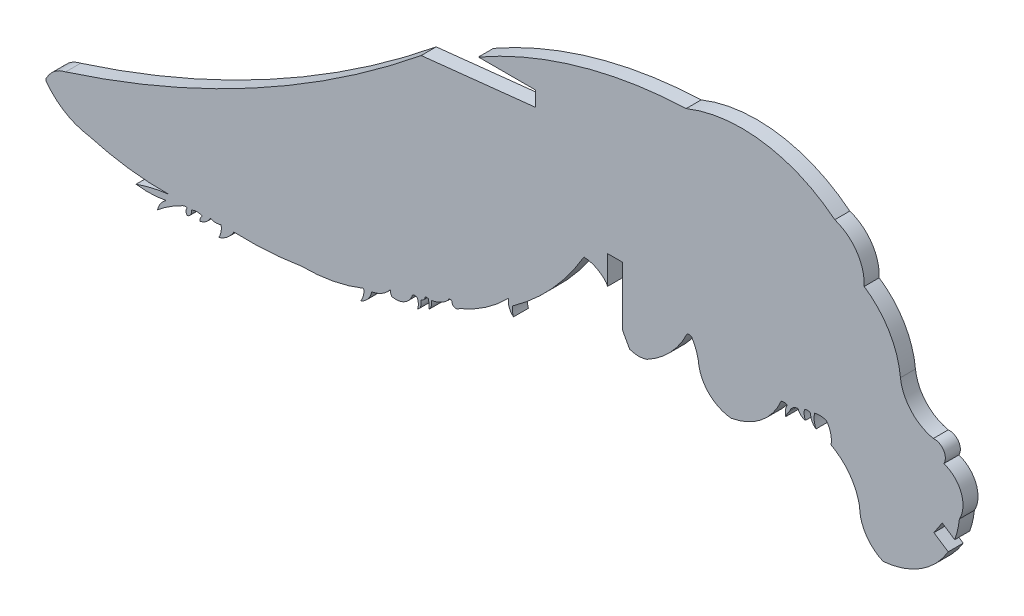
SolidWorks part; units mm, degrees
ref_plane "Front Plane" through (0, 0, 0) normal (0, 0, 1) x (1, 0, 0)
ref_plane "Top Plane" through (0, 0, 0) normal (0, 1, 0) x (1, 0, 0)
ref_plane "Right Plane" through (0, 0, 0) normal (1, 0, 0) x (0, 0, -1)
sketch "Sketch1" plane through (0, 0, 0) normal (0, 0, 1) x (1, 0, 0)
  line L0 (52.7499, 70.1318) -> (64.3715, 71.3815)
  line L1 (64.3715, 71.3815) -> (64.3715, 72.9055)
  line L2 (64.3715, 72.9055) -> (58.5607, 72.9055)
  arc A0 (16.6357, 50.6377) -> (52.7499, 70.1318) centre (-16.879, 155.9248) ccw
  arc A1 (58.5607, 72.9055) -> (79.6651, 78.9249) centre (81.4568, 32.6366) cw
  arc A2 (79.6651, 78.9249) -> (94.7592, 76.6935) centre (85.3161, 64.9832) cw
  arc A3 (94.7592, 76.6935) -> (97.7466, 72.3165) centre (93.3504, 72.5239) cw
  arc A4 (97.7466, 72.3165) -> (101.4288, 66.1332) centre (93.0407, 65.3261) cw
  arc A5 (101.4288, 66.1332) -> (104.7636, 62.451) centre (105.6642, 66.6179) ccw
  arc A6 (104.7636, 62.451) -> (105.8344, 60.7757) centre (104.878, 61.3443) cw
  arc A7 (105.8344, 60.7757) -> (107.4136, 56.6954) centre (104.9626, 58.0925) cw
  arc A8 (107.4136, 56.6954) -> (99.6697, 49.0898) centre (98.9655, 57.552) cw
  arc A9 (99.6697, 49.0898) -> (97.2774, 52.7389) centre (101.2688, 52.747) cw
  arc A10 (97.2774, 52.7389) -> (94.3777, 56.6954) centre (91.6801, 51.6775) ccw
  arc A11 (94.3777, 56.6954) -> (93.9114, 58.6026) centre (91.9396, 57.1099) ccw
  arc A12 (93.9114, 58.6026) -> (92.7155, 58.6578) centre (93.2218, 56.6439) ccw
  arc A13 (92.7155, 58.6578) -> (92.8575, 57.3378) centre (94.569, 58.1895) ccw
  arc A14 (92.8575, 57.3378) -> (92.3084, 58.4414) centre (93.5533, 58.3724) cw
  arc A15 (92.3084, 58.4414) -> (91.6801, 58.4762) centre (91.9646, 57.9232) ccw
  arc A16 (91.6801, 58.4762) -> (91.7794, 57.552) centre (93.0965, 58.1611) ccw
  arc A17 (91.7794, 57.552) -> (91.0329, 58.2279) centre (91.9297, 58.4683) cw
  arc A18 (91.0329, 58.2279) -> (90.1702, 57.5697) centre (91.1217, 57.2172) ccw
  arc A19 (90.1702, 57.5697) -> (89.7788, 56.8792) centre (91.7217, 56.2341) ccw
  arc A20 (89.7788, 56.8792) -> (89.9407, 57.9851) centre (91.1279, 57.2465) cw
  arc A21 (89.9407, 57.9851) -> (89.3088, 58.0044) centre (89.6037, 57.3052) ccw
  arc A22 (89.3088, 58.0044) -> (84.2372, 53.9696) centre (83.0444, 60.6738) cw
  arc A23 (84.2372, 53.9696) -> (80.9686, 56.8792) centre (84.55, 57.6117) cw
  arc A24 (80.9686, 56.8792) -> (80.2253, 59.1108) centre (75.9214, 56.4377) ccw
  arc A25 (80.2253, 59.1108) -> (79.7482, 59.1337) centre (79.9709, 58.7913) ccw
  arc A26 (79.7482, 59.1337) -> (75.7005, 54.8813) centre (71.2227, 63.1961) cw
  arc A27 (75.7005, 54.8813) -> (73.9294, 54.8813) centre (74.8149, 57.3024) cw
  arc A28 (73.9294, 54.8813) -> (71.5552, 59.5421) centre (124.0127, 83.3286) cw
  arc A29 (71.5552, 59.5421) -> (69.2804, 60.6738) centre (69.0881, 57.4352) ccw
  arc A30 (69.2804, 60.6738) -> (62.0239, 52.7389) centre (47.2299, 73.5536) cw
  arc A31 (62.0239, 52.7389) -> (62.1223, 51.8245) centre (63.9478, 52.4833) ccw
  arc A32 (62.1223, 51.8245) -> (61.6182, 53.2211) centre (63.0669, 52.9546) cw
  arc A33 (61.6182, 53.2211) -> (56.6231, 49.804) centre (51.0045, 63.3771) cw
  arc A34 (56.6231, 49.804) -> (55.8555, 50.0753) centre (56.2872, 50.0753) cw
  arc A35 (55.8555, 50.0753) -> (55.4917, 49.9671) centre (55.6916, 49.9608) ccw
  arc A36 (55.4917, 49.9671) -> (53.7982, 49.1144) centre (53.3136, 52.185) cw
  arc A37 (53.7982, 49.1144) -> (53.5348, 48.1955) centre (52.8025, 48.9026) cw
  arc A38 (53.5348, 48.1955) -> (53.4852, 49.0898) centre (50.4012, 48.4703) ccw
  arc A39 (53.4852, 49.0898) -> (53.1314, 49.0898) centre (53.3083, 48.7282) ccw
  arc A40 (53.1314, 49.0898) -> (52.7004, 48.6445) centre (52.686, 49.0896) cw
  arc A41 (52.7004, 48.6445) -> (52.3792, 47.631) centre (51.8916, 48.3432) cw
  arc A42 (52.3792, 47.631) -> (52.3792, 48.5846) centre (51.0179, 48.1078) ccw
  arc A43 (52.3792, 48.5846) -> (51.8644, 48.6221) centre (52.0989, 48.2886) ccw
  arc A44 (51.8644, 48.6221) -> (49.7753, 47.4333) centre (50.1742, 49.1623) cw
  arc A45 (49.7753, 47.4333) -> (49.6202, 47.9709) centre (50.4475, 47.9183) cw
  arc A46 (49.6202, 47.9709) -> (47.7278, 46.8343) centre (47.2107, 49.8391) cw
  arc A47 (47.7278, 46.8343) -> (46.5945, 45.465) centre (45.8685, 47.2194) cw
  arc A48 (46.5945, 45.465) -> (46.9062, 46.7307) centre (45.245, 46.4685) ccw
  arc A49 (46.9062, 46.7307) -> (40.5712, 45.519) centre (40.7078, 61.9707) cw
  arc A50 (40.5712, 45.519) -> (33.7256, 45.091) centre (35.0703, 78.5397) cw
  arc A51 (33.7256, 45.091) -> (32.1786, 43.8381) centre (31.332, 46.465) cw
  arc A52 (32.1786, 43.8381) -> (32.4172, 45.091) centre (30.7321, 44.7628) ccw
  arc A53 (32.4172, 45.091) -> (31.332, 45.1029) centre (31.8889, 46.3985) cw
  arc A54 (31.332, 45.1029) -> (30.2591, 44.3202) centre (30.0104, 45.7879) cw
  arc A55 (30.2591, 44.3202) -> (30.5312, 44.8641) centre (30.9036, 44.3378) cw
  arc A56 (30.5312, 44.8641) -> (29.429, 44.8641) centre (29.9801, 43.8994) ccw
  arc A57 (29.429, 44.8641) -> (28.9896, 44.1659) centre (28.811, 44.7657) cw
  arc A58 (28.9896, 44.1659) -> (28.9896, 44.8641) centre (29.4126, 44.515) cw
  arc A59 (28.9896, 44.8641) -> (28.3089, 44.6783) centre (28.8452, 44.0538) ccw
  arc A60 (28.3089, 44.6783) -> (25.9554, 43.1433) centre (32.7349, 35.3202) ccw
  arc A61 (25.9554, 43.1433) -> (26.8572, 44.4324) centre (28.0271, 42.654) cw
  arc A62 (26.8572, 44.4324) -> (23.7914, 44.3332) centre (25.0508, 52.84) cw
  arc A63 (23.7914, 44.3332) -> (27.0799, 45.1024) centre (28.8756, 30.0119) cw
  arc A64 (27.0799, 45.1024) -> (19.0459, 46.176) centre (26.6912, 72.7911) cw
  arc A65 (16.6357, 50.6377) -> (14.7526, 49.2272) centre (17.2252, 47.8885) ccw
  arc A66 (19.0459, 46.176) -> (14.7526, 48.6963) centre (19.9879, 52.6976) cw
  arc A67 (14.7526, 48.6963) -> (14.7526, 49.2272) centre (15.0105, 48.9617) cw
extrude "Boss-Extrude1" add sketch "Sketch1" along normal blind 1.524
sketch "Sketch2" plane through (0, 0, 1.524) normal (0, 0, 1) x (1, 0, 0)
  line L0 (106.9405, 54.636) -> (105.6657, 55.4759)
  line L1 (106.3971, 53.1691) -> (104.8273, 54.2032)
  line L2 (105.6657, 55.4759) -> (104.8273, 54.2032)
  line L3 (106.1021, 53.3634) -> (104.8273, 54.2032) construction
  line L4 (106.9405, 54.636) -> (106.3971, 53.1691)
  line L5 (73.1978, 56.2096) -> (73.1978, 62.1762)
  line L6 (73.1978, 62.1762) -> (71.6738, 62.1762)
  line L7 (71.6738, 62.1762) -> (71.6738, 56.2096)
  line L8 (71.6738, 56.2096) -> (73.1978, 56.2096)
  arc A0 (99.6697, 49.0898) -> (107.4136, 56.6954) centre (98.9655, 57.552) ccw construction
  arc A2 (71.5552, 59.5421) -> (73.9294, 54.8813) centre (124.0127, 83.3286) ccw construction
  dimension "D1" = 1.524
extrude "Cut-Extrude3" cut sketch "Sketch2" against normal through all contours L7 L8 L5 L6 | L4 L0 L2 L1
